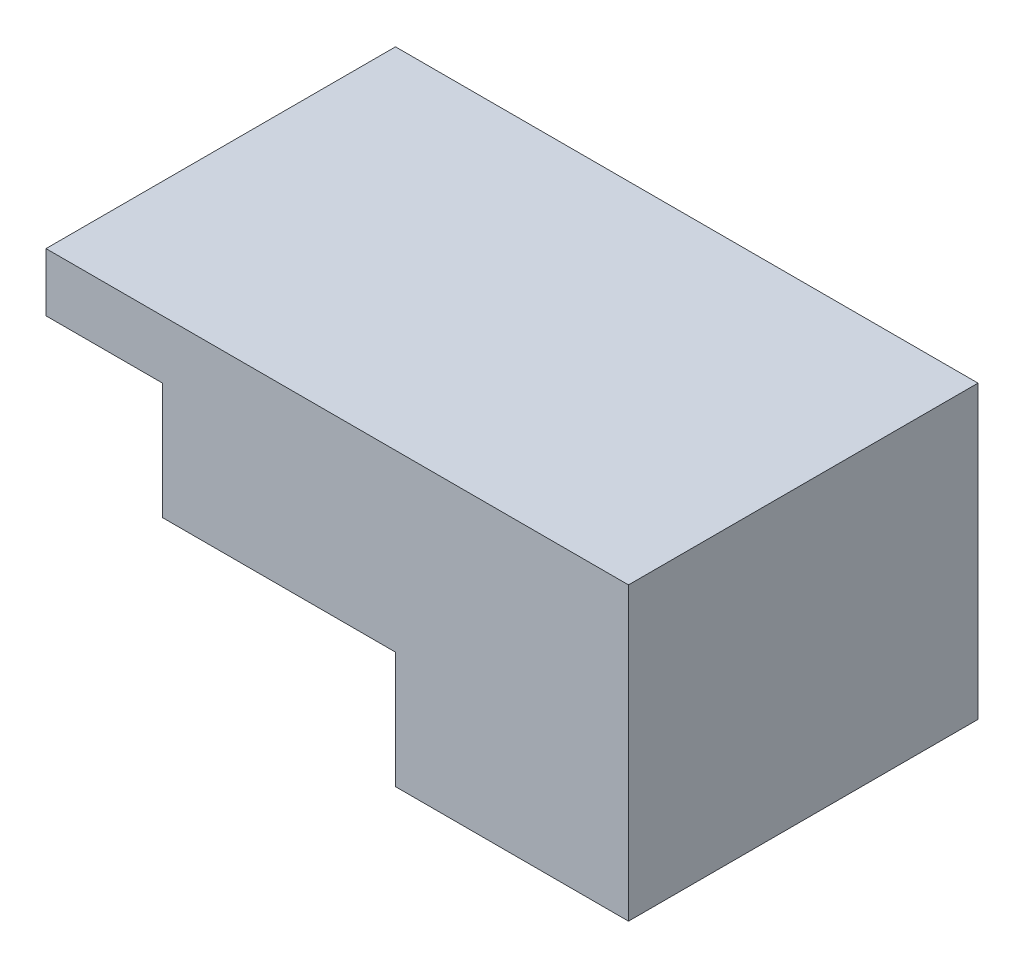
SolidWorks part; units mm, degrees
ref_plane "Front Plane" through (0, 0, 0) normal (0, 0, 1) x (1, 0, 0)
ref_plane "Top Plane" through (0, 0, 0) normal (0, 1, 0) x (1, 0, 0)
ref_plane "Right Plane" through (0, 0, 0) normal (1, 0, 0) x (0, 0, -1)
sketch "Sketch1" plane through (0, 0, 0) normal (0, 0, 1) x (1, 0, 0)
  line L1 (0, 0) -> (0, -50.8)
  line L2 (0, -50.8) -> (101.6, -50.8)
  line L3 (101.6, -50.8) -> (101.6, 76.2)
  line L4 (101.6, 76.2) -> (-152.4, 76.2)
  line L5 (-152.4, 76.2) -> (-152.4, 50.8)
  line L6 (-152.4, 50.8) -> (-101.6, 50.8)
  line L7 (-101.6, 50.8) -> (-101.6, 0)
  line L8 (-101.6, 0) -> (0, 0)
  dimension "D1" = 127
  dimension "D2" = 101.6
  dimension "D3" = 50.8
  dimension "D4" = 101.6
  dimension "D5" = 50.8
  dimension "D6" = 50.8
extrude "Boss-Extrude3" add sketch "Sketch1" against normal blind 152.4
